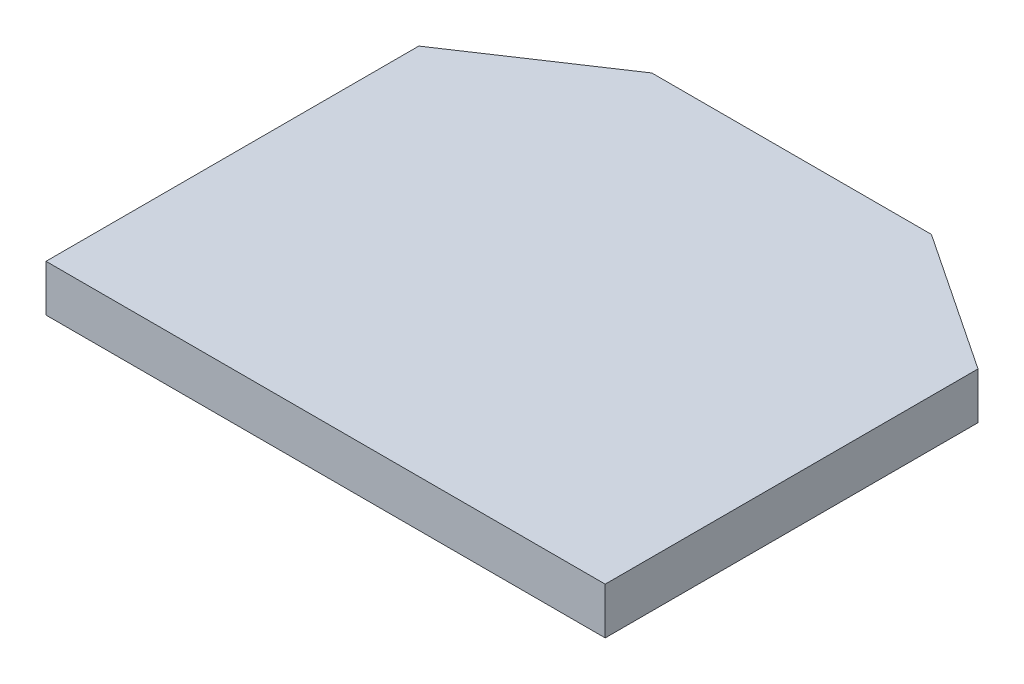
SolidWorks part; units mm, degrees
material "Acrylic (Medium-high impact)"
ref_plane "Front Plane" through (0, 0, 0) normal (0, 0, 1) x (1, 0, 0)
ref_plane "Top Plane" through (0, 0, 0) normal (0, 1, 0) x (1, 0, 0)
ref_plane "Right Plane" through (0, 0, 0) normal (1, 0, 0) x (0, 0, -1)
sketch "Sketch2" plane through (0, 0, 0) normal (0, 1, 0) x (1, 0, 0)
  line L0 (-38.1, 0) -> (38.1, 0)
  line L1 (-38.1, 0) -> (-38.1, 50.8)
  line L2 (38.1, 0) -> (38.1, 50.8)
  line L3 (0, 0) -> (0, 63.5) construction
  line L4 (-19.05, 63.5) -> (19.05, 63.5)
  line L7 (-38.1, 50.8) -> (-19.05, 63.5)
  line L8 (19.05, 63.5) -> (38.1, 50.8)
  point P4 (0, 0)
  point P12 (0, 63.5)
extrude "Boss-Extrude1" add sketch "Sketch2" along normal blind 6.35 contours L0 L2 L8 L4 L7 L1
